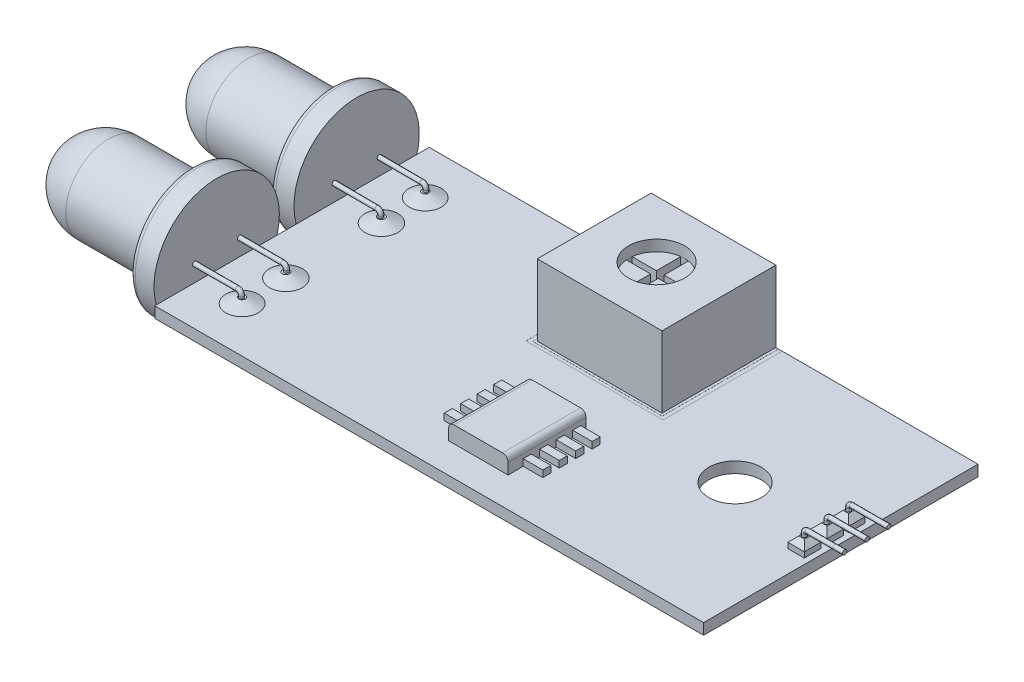
SolidWorks part; units mm, degrees
ref_plane "Front Plane" through (0, 0, 0) normal (0, 0, 1) x (1, 0, 0)
ref_plane "Top Plane" through (0, 0, 0) normal (0, 1, 0) x (1, 0, 0)
ref_plane "Right Plane" through (0, 0, 0) normal (1, 0, 0) x (0, 0, -1)
sketch "Sketch2" plane through (0, 0, 0) normal (0, 1, 0) x (1, 0, 0)
  line L1 (0, 0) -> (25.4, 0)
  line L2 (0, 0) -> (0, 12.7)
  line L3 (0, 12.7) -> (25.4, 12.7)
  line L4 (25.4, 0) -> (25.4, 12.7)
  dimension "D1" = 12.7
  dimension "D2" = 25.4
extrude "Boss-Extrude1" add sketch "Sketch2" along normal blind 0.508
sketch "Sketch3" plane through (0, 0.508, 0) normal (0, 1, 0) x (1, 0, 0)
  line L0 (0, 6.35) -> (25.4, 6.35) construction
  line L1 (0, 12.7) -> (0, 0) construction
  line L2 (25.4, 0) -> (25.4, 12.7) construction
  line L3 (25.146, 7.729) -> (24.384, 7.729)
  line L4 (25.146, 6.7293) -> (24.384, 6.7293)
  line L5 (25.146, 6.7293) -> (25.146, 5.9673)
  line L6 (25.146, 5.9673) -> (24.384, 5.9673)
  line L7 (24.384, 6.7293) -> (24.384, 5.9673)
  line L8 (25.146, 7.729) -> (25.146, 6.967)
  line L9 (25.146, 6.967) -> (24.384, 6.967)
  line L10 (24.384, 7.729) -> (24.384, 6.967)
  line L11 (25.146, 5.6788) -> (24.384, 5.6788)
  line L12 (25.146, 5.6788) -> (25.146, 4.9168)
  line L13 (25.146, 4.9168) -> (24.384, 4.9168)
  line L14 (24.384, 5.6788) -> (24.384, 4.9168)
  dimension "D1" = 0.762
  dimension "D2" = 0.762
  dimension "D3" = 0.254
  dimension "D4" = 0.254
  dimension "D5" = 0.254
extrude "Boss-Extrude2" add sketch "Sketch3" along normal blind 0.508 and the other way blind 0.5334
sketch "Sketch4" plane through (0, -0.0254, 0) normal (0, -1, 0) x (1, 0, 0)
  line L0 (25.146, -7.348) -> (24.384, -7.348) construction
  line L1 (25.146, -7.729) -> (25.146, -6.967) construction
  line L2 (24.384, -7.729) -> (24.384, -6.967) construction
  circle A0 centre (24.765, -7.348) radius 0.3229
  circle A1 centre (24.765, -6.332) radius 0.3229
  circle A2 centre (24.765, -5.316) radius 0.3229
extrude "Boss-Extrude3" add sketch "Sketch4" along normal blind 2.54 draft 45
ref_plane "Plane1" through (0, 0, -5.2978) normal (0, 0, 1) x (1, 0, 0)
ref_plane "Plane2" through (0, 0, -6.3483) normal (0, 0, 1) x (1, 0, 0)
ref_plane "Plane3" through (0, 0, -7.348) normal (0, 0, 1) x (1, 0, 0)
sketch "Sketch5" plane through (0, 0, -5.2978) normal (0, 0, 1) x (1, 0, 0)
  line L0 (24.765, 0) -> (24.765, 1.1529)
  line L1 (25.146, 0) -> (24.384, 0) construction
  line L2 (24.902, 1.2898) -> (26.181, 1.2898)
  line L3 (26.181, 1.2898) -> (26.6288, 1.2898)
  arc A0 (24.765, 1.1529) -> (24.902, 1.2898) centre (24.902, 1.1529) cw
sweep "Sweep1" add path "Sketch5" circular profile diameter 0.2032 parameters "D3"=0.2032
sketch "Sketch26" plane through (0, 0, -6.3483) normal (0, 0, 1) x (1, 0, 0)
  line L0 (24.765, 0) -> (24.765, 1.1529)
  line L1 (25.146, 0) -> (24.384, 0) construction
  line L2 (24.6634, 1.1529) -> (24.8666, 1.1529) construction
  line L3 (24.902, 1.3914) -> (24.902, 1.1882) construction
  line L4 (24.902, 1.2898) -> (26.6288, 1.2898)
  arc A0 (24.765, 1.1529) -> (24.902, 1.2898) centre (24.902, 1.1529) cw
sweep "Sweep2" add path "Sketch26" circular profile diameter 0.2032 parameters "D3"=0.2032
sketch "Sketch41" plane through (0, 0, -7.348) normal (0, 0, 1) x (1, 0, 0)
  line L0 (24.765, 0) -> (24.765, 1.1529)
  line L1 (24.384, 0) -> (25.146, 0) construction
  line L2 (24.8666, 1.1529) -> (24.6634, 1.1529) construction
  line L3 (24.902, 1.1882) -> (24.902, 1.3914) construction
  line L4 (24.902, 1.2898) -> (26.6288, 1.2898)
  line L5 (26.6288, 1.1882) -> (26.6288, 1.3914) construction
  arc A0 (24.765, 1.1529) -> (24.902, 1.2898) centre (24.902, 1.1529) cw
sweep "Sweep3" add path "Sketch41" circular profile diameter 0.2032 parameters "D3"=0.2032
chamfer "Chamfer1" distance 0.254 angle 45 12 edges at (25.146, 1.016, -5.2978) (24.765, 1.016, -4.9168) (24.384, 1.016, -5.2978) (24.765, 1.016, -5.6788) (25.146, 1.016, -6.3483) (24.765, 1.016, -5.9673) (24.384, 1.016, -6.3483) (24.765, 1.016, -6.7293) (24.765, 1.016, -6.967) (25.146, 1.016, -7.348) (24.384, 1.016, -7.348) (24.765, 1.016, -7.729)
sketch "Sketch56" plane through (0, 0.508, 0) normal (0, 1, 0) x (1, 0, 0)
  line L0 (0, 6.35) -> (9.188, 6.35) construction
  line L1 (0, 12.7) -> (0, 0) construction
  line L2 (1.9274, 8.5598) -> (1.9274, 10.5891)
  circle A0 centre (1.9274, 10.5891) radius 0.7506
  circle A1 centre (1.9274, 8.5598) radius 0.762
  circle A2 centre (1.9274, 2.1109) radius 0.7506
  circle A3 centre (1.9274, 4.1402) radius 0.762
  dimension "D1" = 1.5011
  dimension "D2" = 1.524
extrude "Boss-Extrude4" add sketch "Sketch56" along normal blind 0.254 draft 67
sketch "Sketch57" plane through (0, 0.508, 0) normal (0, 1, 0) x (1, 0, 0)
  line L0 (25.4, 12.7) -> (0, 12.7) construction
  line L1 (10.2704, 12.7) -> (16.0428, 12.7)
  line L2 (10.2704, 12.7) -> (10.2704, 7.4323)
  line L3 (10.2704, 7.4323) -> (16.0428, 7.4323)
  line L4 (16.0428, 12.7) -> (16.0428, 7.4323)
extrude "Boss-Extrude5" add sketch "Sketch57" along normal blind 3.302
sketch "Sketch58" plane through (0, 3.81, 0) normal (0, 1, 0) x (1, 0, 0)
  line L4 (12.9926, 9.954) -> (12.9926, 8.7849)
  line L5 (12.9926, 11.3474) -> (12.9926, 10.2204)
  line L7 (13.3479, 11.3436) -> (13.3479, 10.2204)
  line L8 (11.8742, 10.2204) -> (12.9926, 10.2204)
  line L9 (13.3479, 9.954) -> (13.3479, 8.7887)
  line L10 (11.8698, 9.954) -> (12.9926, 9.954)
  line L11 (13.3479, 10.2204) -> (14.439, 10.2204)
  line L13 (13.3479, 9.954) -> (14.4434, 9.954)
  arc A0 (12.9926, 8.7849) -> (13.3479, 8.7887) centre (13.1566, 10.0662) ccw
  arc A1 (14.4434, 9.954) -> (14.439, 10.2204) centre (13.1566, 10.0662) ccw
  arc A2 (13.3479, 11.3436) -> (12.9926, 11.3474) centre (13.1566, 10.0662) ccw
  arc A3 (11.8742, 10.2204) -> (11.8698, 9.954) centre (13.1566, 10.0662) ccw
extrude "Cut-Extrude1" cut sketch "Sketch58" against normal blind 1.27
sketch "Sketch59" plane through (0, 3.81, 0) normal (0, 1, 0) x (1, 0, 0)
  circle A0 centre (13.1566, 10.0662) radius 1.2954
  dimension "D1" = 2.5908
extrude "Cut-Extrude2" cut sketch "Sketch59" against normal blind 0.508
sketch "Sketch60" plane through (0, 0.508, 0) normal (0, 1, 0) x (1, 0, 0)
  line L0 (10.2704, 12.7) -> (0, 12.7) construction
  line L1 (10.1594, 12.7) -> (16.1636, 12.7)
  line L2 (10.1594, 12.7) -> (10.1594, 7.3217)
  line L3 (10.1594, 7.3217) -> (16.1636, 7.3217)
  line L4 (16.1636, 12.7) -> (16.1636, 7.3217)
  line L6 (9.9995, 12.7) -> (16.3412, 12.7)
  line L7 (9.9995, 12.7) -> (9.9995, 7.1796)
  line L8 (9.9995, 7.1796) -> (16.3412, 7.1796)
  line L9 (16.3412, 12.7) -> (16.3412, 7.1796)
  line M18 (10.2704, 12.7) -> (0, 12.7)
  line M22 (25.4, 12.7) -> (16.0428, 12.7)
extrude "Cut-Extrude3" cut sketch "Sketch60" against normal blind 0.0025 contours L9 L4 L3 L2 L7 L8 M22 M18
sketch "Sketch61" plane through (0, 0.508, 0) normal (0, 1, 0) x (1, 0, 0)
  line L0 (-0.1397, 6.3483) -> (0.1397, 6.3483) construction
  circle A0 centre (20.5074, 6.3483) radius 1.2159
extrude "Cut-Extrude4" cut sketch "Sketch61" against normal through all
sketch "Sketch62" plane through (0, 0.508, 0) normal (0, 1, 0) x (1, 0, 0)
  line L1 (12.2095, 4.9971) -> (14.9605, 4.9971)
  line L2 (12.2095, 4.9971) -> (12.2095, 1.3893)
  line L3 (12.2095, 1.3893) -> (14.9605, 1.3893)
  line L4 (14.9605, 4.9971) -> (14.9605, 1.3893)
extrude "Boss-Extrude6" add sketch "Sketch62" along normal blind 0.762
sketch "Sketch63" plane through (0, 0.508, 0) normal (0, 1, 0) x (1, 0, 0)
  line L0 (12.2095, 4.9971) -> (12.2095, 1.3893) construction
  line L1 (12.2095, 4.7493) -> (11.3043, 4.7493)
  line L2 (12.2095, 4.7493) -> (12.2095, 4.3762)
  line L3 (12.2095, 4.3762) -> (11.3043, 4.3762)
  line L4 (11.3043, 4.7493) -> (11.3043, 4.3762)
  line L5 (12.2095, 3.9873) -> (12.2095, 3.6142)
  line L6 (12.2095, 3.9873) -> (11.3043, 3.9873)
  line L7 (11.3043, 3.9873) -> (11.3043, 3.6142)
  line L8 (12.2095, 3.6142) -> (11.3043, 3.6142)
  line L9 (12.2095, 3.2253) -> (12.2095, 2.8522)
  line L10 (12.2095, 3.2253) -> (11.3043, 3.2253)
  line L11 (11.3043, 3.2253) -> (11.3043, 2.8522)
  line L12 (12.2095, 2.8522) -> (11.3043, 2.8522)
  line L13 (12.2095, 2.4633) -> (12.2095, 2.0902)
  line L14 (12.2095, 2.4633) -> (11.3043, 2.4633)
  line L15 (11.3043, 2.4633) -> (11.3043, 2.0902)
  line L16 (12.2095, 2.0902) -> (11.3043, 2.0902)
  line L17 (13.585, 4.9971) -> (13.585, 1.3893) construction
  line L18 (14.9605, 4.9971) -> (12.2095, 4.9971) construction
  line L19 (12.2095, 1.3893) -> (14.9605, 1.3893) construction
  line L20 (14.9605, 2.0902) -> (15.8657, 2.0902)
  line L21 (15.8657, 2.4633) -> (15.8657, 2.0902)
  line L22 (14.9605, 2.4633) -> (15.8657, 2.4633)
  line L23 (14.9605, 2.4633) -> (14.9605, 2.0902)
  line L24 (14.9605, 2.8522) -> (15.8657, 2.8522)
  line L25 (15.8657, 3.2253) -> (15.8657, 2.8522)
  line L26 (14.9605, 3.2253) -> (15.8657, 3.2253)
  line L27 (14.9605, 3.2253) -> (14.9605, 2.8522)
  line L28 (14.9605, 3.6142) -> (15.8657, 3.6142)
  line L29 (15.8657, 3.9873) -> (15.8657, 3.6142)
  line L30 (14.9605, 3.9873) -> (15.8657, 3.9873)
  line L31 (14.9605, 3.9873) -> (14.9605, 3.6142)
  line L32 (15.8657, 4.7493) -> (15.8657, 4.3762)
  line L33 (14.9605, 4.3762) -> (15.8657, 4.3762)
  line L34 (14.9605, 4.7493) -> (14.9605, 4.3762)
  line L35 (14.9605, 4.7493) -> (15.8657, 4.7493)
extrude "Boss-Extrude7" add sketch "Sketch63" along normal blind 0.3048
fillet "Fillet1" radius 0.254 2 edges at (12.2095, 1.27, -3.1932) (14.9605, 1.27, -3.1932)
ref_plane "Plane4" through (0, 0, -2.0828) normal (0, 0, 1) x (1, 0, 0)
ref_plane "Plane5" through (0, 0, -4.1656) normal (0, 0, 1) x (1, 0, 0)
sketch "Sketch64" plane through (0, 0, -2.0828) normal (0, 0, 1) x (1, 0, 0)
  line L0 (1.9274, 0.8583) -> (1.9274, 0.2068)
  line L1 (1.7516, 1.0341) -> (-0.5733, 1.0341)
  arc A0 (1.9274, 0.8583) -> (1.7516, 1.0341) centre (1.7516, 0.8583) ccw
sweep "Sweep4" add path "Sketch64" circular profile diameter 0.2032 parameters "D3"=0.2032
sketch "Sketch79" plane through (0, 0, -4.1656) normal (0, 0, 1) x (1, 0, 0)
  line L0 (1.9274, 0.8583) -> (1.9274, 0.2236)
  line L1 (2.029, 0.8583) -> (1.8258, 0.8583) construction
  line L2 (1.7516, 1.1357) -> (1.7516, 0.9325) construction
  line L3 (1.7516, 1.0341) -> (-0.5733, 1.0341)
  arc A0 (1.9274, 0.8583) -> (1.7516, 1.0341) centre (1.7516, 0.8583) ccw
sweep "Sweep5" add path "Sketch79" circular profile diameter 0.2032 parameters "D3"=0.2032
ref_plane "Plane6" through (0, 0, -3.0988) normal (0, 0, 1) x (1, 0, 0)
sketch "Sketch94" plane through (0, 0, -3.0988) normal (0, 0, 1) x (1, 0, 0)
  line L0 (-0.2357, 1.048) -> (-0.2357, 3.9475)
  line L1 (-5.2534, 3.0117) -> (-1.3573, 3.0117)
  line L2 (-1.3573, 3.0117) -> (-1.3573, 3.9475)
  line L3 (-1.3573, 3.9475) -> (-0.2357, 3.9475)
  line L4 (-7.4618, 1.048) -> (-0.2357, 1.048)
  line L5 (-0.2357, 1.048) -> (-11.2422, 1.048) construction
  arc A0 (-5.2534, 3.0117) -> (-7.4618, 1.048) centre (-5.2534, 0.7882) ccw
revolve "Revolve1" add sketch "Sketch94" angle 360 about L5
fillet "Fillet2" radius 0.254 2 edges at (-1.3573, 1.048, -5.9982) (-1.3573, 1.048, -5.0625)
ref_plane "Plane7" through (0, 0, -10.6172) normal (0, 0, -1) x (-1, 0, 0)
ref_plane "Plane8" through (0, 0, -8.5344) normal (0, 0, -1) x (-1, 0, 0)
sketch "Sketch95" plane through (0, 0, -8.5344) normal (0, 0, -1) x (-1, 0, 0)
  line L0 (-1.9274, 0.8583) -> (-1.9274, 0.2244)
  line L1 (-2.029, 0.8583) -> (-1.8258, 0.8583) construction
  line L2 (-1.7516, 1.1357) -> (-1.7516, 0.9325) construction
  line L3 (-1.7516, 1.0341) -> (1.1033, 1.048)
  line L4 (1.1033, -1.8514) -> (1.1033, 3.9475) construction
  arc A0 (-1.9274, 0.8583) -> (-1.7516, 1.0341) centre (-1.7516, 0.8583) cw
sweep "Sweep6" add path "Sketch95" circular profile diameter 0.2032 parameters "D3"=0.2032
sketch "Sketch110" plane through (0, 0, -10.6172) normal (0, 0, -1) x (-1, 0, 0)
  line L0 (-1.9274, 0.8583) -> (-1.9274, 0.2814)
  line L1 (-2.029, 0.8583) -> (-1.8258, 0.8583) construction
  line L2 (-1.7522, 1.0334) -> (1.1033, 1.048)
  line L3 (1.1038, 0.9464) -> (1.1028, 1.1496) construction
  arc A0 (-1.9274, 0.8583) -> (-1.7522, 1.0334) centre (-1.7522, 0.8583) cw
sweep "Sweep7" add path "Sketch110" circular profile diameter 0.2032 parameters "D3"=0.2032
ref_plane "Plane9" through (0, 0, -9.5758) normal (0, 0, -1) x (-1, 0, 0)
sketch "Sketch125" plane through (0, 0, -9.5758) normal (0, 0, -1) x (-1, 0, 0)
  line L0 (7.4618, 1.048) -> (-4.1255, 1.048) construction
  line L1 (0.2211, 1.048) -> (0.2357, 3.9475)
  line L2 (0.2357, 3.9475) -> (0.2357, -1.8514) construction
  line L3 (0.2357, 3.9475) -> (1.3361, 3.9475)
  line L4 (1.3361, 3.9475) -> (1.3573, 3.0117)
  line L5 (1.3573, -1.5974) -> (1.3573, 3.6935) construction
  line L6 (1.3573, 3.0117) -> (5.2534, 3.0117)
  line L7 (5.2534, 3.0117) -> (1.6113, 3.0117) construction
  line L8 (7.4618, 1.048) -> (0.2211, 1.048)
  line L9 (0.2211, 1.048) -> (0.2022, 1.0619)
  arc A0 (5.2534, 3.0117) -> (7.4618, 1.048) centre (5.2534, 0.7882) cw
revolve "Revolve2" add sketch "Sketch125" angle 360 about L0
fillet "Fillet3" radius 0.254 2 edges at (-1.3361, 1.048, -6.6764) (-1.3573, 1.048, -7.6121)
